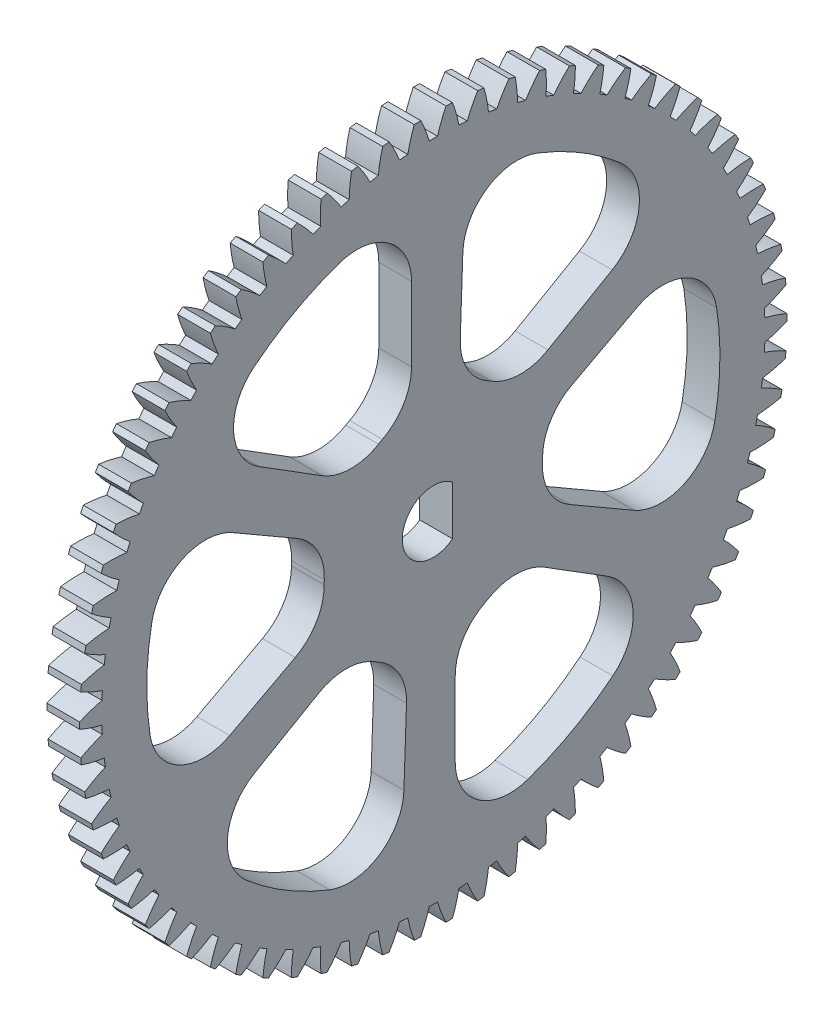
SolidWorks part; units mm, degrees
ref_plane "Plane1" through (0, 0, 0) normal (0, 0, 1) x (1, 0, 0)
ref_plane "Plane2" through (0, 0, 0) normal (0, 1, 0) x (1, 0, 0)
ref_plane "Plane3" through (0, 0, 0) normal (1, 0, 0) x (0, 0, -1)
sketch "HoldingSke" plane through (0, 0, 0) normal (0, 1, 0) x (1, 0, 0)
  line L0 (0, 0) -> (0.38, -1.0441)
  line L1 (-15, 0) -> (100, 0) construction
  line L2 (0, 0) -> (-2.1039, 2.3779)
  line L3 (0, 0) -> (-11.863, 4.5341)
  line L4 (0, 0) -> (2.9537, 8.1152)
  line L5 (0, 0) -> (-46.8476, -17.4728)
  line L6 (0, 0) -> (-2.4869, -1.6779)
  line L7 (-2.1039, 2.3779) -> (8.6589, 51.2072)
  line L8 (-76.2, 54.61) -> (-75.2, 54.61)
  line L9 (-71.009, 38.7566) -> (-53.1078, 45.2721)
  line L10 (-76.2, 71.12) -> (104.1128, 71.12)
  line L11 (0, 0) -> (-3, 0)
  line L12 (-76.2, 101.6) -> (-76.166, 101.6)
  line L13 (24.9733, 27.94) -> (52.9518, 28.4284)
  line L14 (24.9733, 27.94) -> (24.9743, 27.94)
  line L15 (24.9733, 27.94) -> (100.4006, 29.5858)
  line L16 (-63.627, -0.9) -> (-12.827, -0.9)
  circle A0 centre (0, 0) radius 3
  circle A1 centre (0, 0) radius 30.374
  circle A2 centre (0, 0) radius 37.5
  circle A3 centre (0, 0) radius 3
  dimension "MHD" = 60.748
  dimension "Hub_dia" = 75
  dimension "Bore" = 6
  dimension "MBD" = 6
  dimension "Num_teeth" = 70
  dimension "Pitch" = 1.1111
  dimension "Overall_len" = 50
  dimension "Show_teeth" = 70
  dimension "Thickness" = 3
  dimension "OAL" = 50.0014
  dimension "T_dim" = 1
  dimension "Ap" = 20
  dimension "H" = 19.05
  dimension "Pitch_radius" = 180.3128
  dimension "Width" = 3
  dimension "Backlash" = 0.034
  dimension "Addendum_fac" = 1
  dimension "Dedendum_fac" = 1.25
  dimension "Clearance_fac" = 0.25
  dimension "Dedendum_add" = 0.001
  dimension "Module" = 0.9
sketch "BasProSke" plane through (0, 0, 0) normal (0, 1, 0) x (1, 0, 0)
  line L0 (-10, 0) -> (60, 0) construction
  line L1 (0, 0) -> (0, 32.4)
  line L2 (0, 0) -> (3, 0)
  line L3 (3, 0) -> (3, 32.4)
  line L4 (3, 32.4) -> (0, 32.4)
  dimension "Thickness" = 3
  dimension "Diameter" = 64.8
revolve "Base-Revolve" add sketch "BasProSke" angle 360 about L0
sketch "TooCutSke" plane through (0, 0, 0) normal (1, 0, 0) x (0, 0, -1)
  line L1 (0, 0) -> (0, 107) construction
  line L2 (0, 0) -> (-0.7663, 31.4907) construction
  line L3 (0, 0) -> (-2.8259, 62.9233) construction
  line L4 (-0.7663, 31.4907) -> (-1.4129, 31.4616) construction
  arc A0 (0.3819, 30.3716) -> (-0.3819, 30.3716) centre (0, 0) ccw
  arc A1 (1.1716, 32.4042) -> (-1.1716, 32.4042) centre (0, 0) ccw
  circle A2 centre (0, 0) radius 31.5 construction
  circle A3 centre (0, 0) radius 29.6003 construction
  arc A4 (-0.3819, 30.3716) -> (-1.1716, 32.4042) centre (-12.4774, 26.842) ccw
  arc A5 (1.1716, 32.4042) -> (0.3819, 30.3716) centre (12.4774, 26.842) ccw
  dimension "Root_dia" = 60.748
  dimension "Overcut_dia" = 64.8508
  dimension "Pitch_dia" = 63
  dimension "Base_dia" = 59.2006
  dimension "Flank_rad" = 12.6
  dimension "Half_ang" = 2.571
  dimension "Half_CT" = 0.6473
extrude "ToothCut" cut sketch "TooCutSke" along normal through all
fillet "Breaks" [suppressed] radius 0.018
fillet "RootFillets" [suppressed] radius 0.226
pattern_circular "TeethCuts" count 70 every 5.143 about axis through (-10, 0, 0) along (1, 0, 0) of "ToothCut", "RootFillets", "Breaks"
sketch "HubNeaOneSke" plane through (0, 0, 0) normal (-1, 0, 0) x (0, 0, 1)
  circle A0 centre (0, 0) radius 30.374
  dimension "Diameter" = 60.748
extrude "HubNearOne" [suppressed] add sketch "HubNeaOneSke" along normal blind 47.0014
sketch "HubNeaBotSke" plane through (0, 0, 0) normal (-1, 0, 0) x (0, 0, 1)
  circle A0 centre (0, 0) radius 30.374
  dimension "Diameter" = 60.748
extrude "HubNearBoth" [suppressed] add sketch "HubNeaBotSke" along normal blind 23.5007
ref_plane "FarPln" through (3, 0, 0) normal (1, 0, 0) x (0, 0, -1)
sketch "HubFarSke" plane through (3, 0, 0) normal (1, 0, 0) x (0, 0, -1)
  circle A0 centre (0, 0) radius 30.374
  dimension "Diameter" = 60.748
extrude "HubFar" [suppressed] add sketch "HubFarSke" along normal blind 23.5007
sketch "KeySke" plane through (0, 0, 0) normal (1, 0, 0) x (0, 0, -1)
  line L0 (-1, 0) -> (-1, 4)
  line L1 (-1, 4) -> (1, 4)
  line L2 (1, 4) -> (1, 0)
  line L3 (0, 0) -> (0, 34) construction
  line L4 (-1, 0) -> (1, 0)
  dimension "Offset" = 4
  dimension "Width" = 2
extrude "Keyway" [suppressed] cut sketch "KeySke" along normal mid plane 100.0028
pattern_circular "Keyway2" [suppressed] count 2 every 90 about axis through (-10, 0, 0) along (1, 0, 0)
sketch "Sketch1" plane through (3, 0, 0) normal (1, 0, 0) x (0, 0, -1)
  line L0 (1.7493, 2.25) -> (1.7493, -2.25)
  arc A0 (1.7493, 2.25) -> (1.7493, -2.25) centre (0, 0) ccw
  dimension "D1" = 5.7
  dimension "D2" = 4.5
extrude "Cut-Extrude1" cut sketch "Sketch1" against normal through all contours A0 L0
sketch "Sketch2" plane through (3, 0, 0) normal (1, 0, 0) x (0, 0, -1)
  line L0 (-2, 9.798) -> (-2, 26.1737)
  line L1 (-7.2493, 6.8882) -> (-21.1367, 15.566)
  arc A1 (-2, 9.798) -> (-7.2493, 6.8882) centre (0, 0) ccw
  arc A2 (-2, 26.1737) -> (-21.1367, 15.566) centre (0, 0) ccw
  dimension "D1" = 2
  dimension "D2" = 20
  dimension "D3" = 52.5
  dimension "D4" = 2
  dimension "D6" = 58
extrude "Cut-Extrude2" cut sketch "Sketch2" against normal through all
pattern_circular "CirPattern3" count 6 every 60 about axis through (0, 0, 0) along (1, 0, 0) of "Cut-Extrude2"
fillet "Fillet1" radius 5 13 edges at (1.5, 6.631, -7.4853) (1.5, -9.7222, 2.3407) (1.5, 3.1669, 9.4853) (1.5, -2.834, 9.59) (1.5, -6.631, 7.4853) (1.5, -9.798, -2) (1.5, -3.1669, -9.4853) (1.5, 2.834, -9.59) (1.5, 9.7222, -2.3407) (1.5, -6.8882, -7.2493) (1.5, 6.8882, 7.2493) (1.5, 9.798, 2) (1.5, 11.3548, 23.6671)
fillet "Fillet2" radius 5 11 edges at (1.5, 26.088, -2.9122) (1.5, 14.8189, -21.6671) (1.5, 10.5219, -24.0489) (1.5, -11.3548, -23.6671) (1.5, -15.566, -21.1367) (1.5, -26.1737, -2) (1.5, -26.088, 2.9122) (1.5, -14.8189, 21.6671) (1.5, -10.5219, 24.0489) (1.5, 15.566, 21.1367) (1.5, 26.1737, 2)
equation "' \"Module@HoldingSke\" = 6.35"
equation "' \"Num_teeth@HoldingSke\" = 12"
equation "' \"Ap@HoldingSke\" =  20"
equation "' \"Ap@HoldingSke\" = 20"
equation "' \"Width@HoldingSke\" = 0.5 * 25.4"
equation "' \"Hub_dia@HoldingSke\"= 1 * 25.4"
equation "' \"Hub_dia@HoldingSke\" = 1 * 25.4"
equation "' \"Overall_len@HoldingSke\" = 1.0 * 25.4"
equation "' \"Bore@HoldingSke\" = 0.75 * 25.4"
equation "' \"T_dim@HoldingSke\" = 0.1 * 25.4"
equation "' \"Width@KeySke\" = 0.25 * 25.4"
equation "' \"Show_teeth@HoldingSke\" = 13"
equation "' \"Backlash@HoldingSke\" = 0.009 * 25.4"
equation "' \"Addendum_fac@HoldingSke\" = 1.0"
equation "' \"Dedendum_fac@HoldingSke\" = 1.25"
equation "' \"Dedendum_add@HoldingSke\" = 0.00005 * 25.4"
equation "' \"Clearance_fac@HoldingSke\" = 0.25"
equation "\"Pitch@HoldingSke\" = 1 / \"Module@HoldingSke\""
equation "\"Overcut_dia@TooCutSke\" = (\"Num_teeth@HoldingSke\" + 2 * \"Addendum_fac@HoldingSke\") / \"Pitch@HoldingSke\" + 0.002 * 25.4"
equation "\"Pitch_dia@TooCutSke\" = \"Num_teeth@HoldingSke\" / \"Pitch@HoldingSke\""
equation "\"Base_dia@TooCutSke\" = \"Num_teeth@HoldingSke\" / \"Pitch@HoldingSke\" * cos((\"Ap@HoldingSke\"  * 3.14159265 / 180))"
equation "\"Root_dia@TooCutSke\" = (\"Num_teeth@HoldingSke\" + 2) / \"Pitch@HoldingSke\" - 2 * (\"Addendum_fac@HoldingSke\" + \"Dedendum_fac@HoldingSke\") / \"Pitch@HoldingSke\" - \"Dedendum_add@HoldingSke\" * 2"
equation "\"Half_ang@TooCutSke\" = 180 / \"Num_teeth@HoldingSke\""
equation "\"Half_CT@TooCutSke\" = \"Num_teeth@HoldingSke\" / \"Pitch@HoldingSke\" * sin((3.14159265 / 2 / \"Num_teeth@HoldingSke\")) / 2 - 7 * \"Backlash@HoldingSke\" / 4"
equation "\"Flank_rad@TooCutSke\" = \"Num_teeth@HoldingSke\" / \"Pitch@HoldingSke\" / 5"
equation "\"Radius@RootFillets\" = \"Clearance_fac@HoldingSke\" / \"Pitch@HoldingSke\" + \"Dedendum_add@HoldingSke\""
equation "\"Break_rad@Breaks\" = 0.02 / \"Pitch@HoldingSke\""
equation "\"Thickness@HoldingSke\" = \"Width@HoldingSke\""
equation "\"OAL@HoldingSke\" = \"Thickness@HoldingSke\""
equation "\"MHD@HoldingSke\" = (\"Num_teeth@HoldingSke\" + 2) / \"Pitch@HoldingSke\" - 2 * (\"Addendum_fac@HoldingSke\" + \"Dedendum_fac@HoldingSke\")  / \"Pitch@HoldingSke\" - \"Dedendum_add@HoldingSke\" * 2"
equation "\"MBD@HoldingSke\" = (\"Num_teeth@HoldingSke\" + 2) / \"Pitch@HoldingSke\" - 2 * (\"Addendum_fac@HoldingSke\" + \"Dedendum_fac@HoldingSke\")  / \"Pitch@HoldingSke\" - \"Dedendum_add@HoldingSke\" * 2 - 0.002 * 25.4"
equation "\"MHD@HoldingSke\" = ((sgn( \"MHD@HoldingSke\" - \"Hub_dia@HoldingSke\" )-1)*( \"MHD@HoldingSke\" - \"Hub_dia@HoldingSke\" ))/-2+ \"Hub_dia@HoldingSke\""
equation "\"MBD@HoldingSke\" = ((sgn( \"MBD@HoldingSke\" - \"Bore@HoldingSke\" )-1)*( \"MBD@HoldingSke\" - \"Bore@HoldingSke\" ))/-2+ \"Bore@HoldingSke\""
equation "\"OAL@HoldingSke\" = ((sgn( \"OAL@HoldingSke\" - \"Overall_len@HoldingSke\" )+1)*( \"OAL@HoldingSke\" - \"Overall_len@HoldingSke\" ))/2 + \"Overall_len@HoldingSke\" + 0.000002 * 25.4"
equation "\"Num_teeth@TeethCuts\" = int( \"Show_teeth@HoldingSke\" ) + 1"
equation "\"Num_teeth@TeethCuts\" = ((sgn( \"Num_teeth@TeethCuts\" - \"Num_teeth@HoldingSke\" )-1)*( \"Num_teeth@TeethCuts\" - \"Num_teeth@HoldingSke\" ))/-2+ \"Num_teeth@HoldingSke\""
equation "\"Num_teeth@TeethCuts\" = ((sgn( \"Num_teeth@TeethCuts\" - 2.0)+1)*( \"Num_teeth@TeethCuts\" - 2.0))/2 +2.0"
equation "\"Angle@TeethCuts\" = 360.0 / \"Num_teeth@HoldingSke\""
equation "\"Diameter@BasProSke\" = (\"Num_teeth@HoldingSke\" + 2 * \"Addendum_fac@HoldingSke\") / \"Pitch@HoldingSke\""
equation "\"Thickness@BasProSke\"  = \"Thickness@HoldingSke\""
equation "' \"Fillet_rad@BasProSke\" =  \"Thickness@HoldingSke\" * 0.05"
equation "' \"Fillet_rad@BasProSke\" = \"Thickness@HoldingSke\" * 0.05"
equation "\"MHD@HoldingSke\" = ((sgn( \"MHD@HoldingSke\" - \"Root_dia@TooCutSke\" )-1)*( \"MHD@HoldingSke\" - \"Root_dia@TooCutSke\" ))/-2+ \"Root_dia@TooCutSke\""
equation "\"Diameter@HubNeaOneSke\" = \"MHD@HoldingSke\""
equation "\"Length@HubNearOne\" = \"OAL@HoldingSke\" - \"Thickness@BasProSke\""
equation "\"Diameter@HubNeaBotSke\" = \"MHD@HoldingSke\""
equation "\"Length@HubNearBoth\" = ( \"OAL@HoldingSke\" - \"Thickness@BasProSke\" ) / 2.0"
equation "\"Thickness@FarPln\" = \"Thickness@BasProSke\""
equation "\"Diameter@HubFarSke\" = \"MHD@HoldingSke\""
equation "\"Length@HubFar\" = ( \"OAL@HoldingSke\" - \"Thickness@BasProSke\" ) / 2.0"
equation "\"D1@Keyway\" = \"OAL@HoldingSke\" * 2.0"
equation "\"Offset@KeySke\" = \"T_dim@HoldingSke\" + \"MBD@HoldingSke\" / 2.0"
